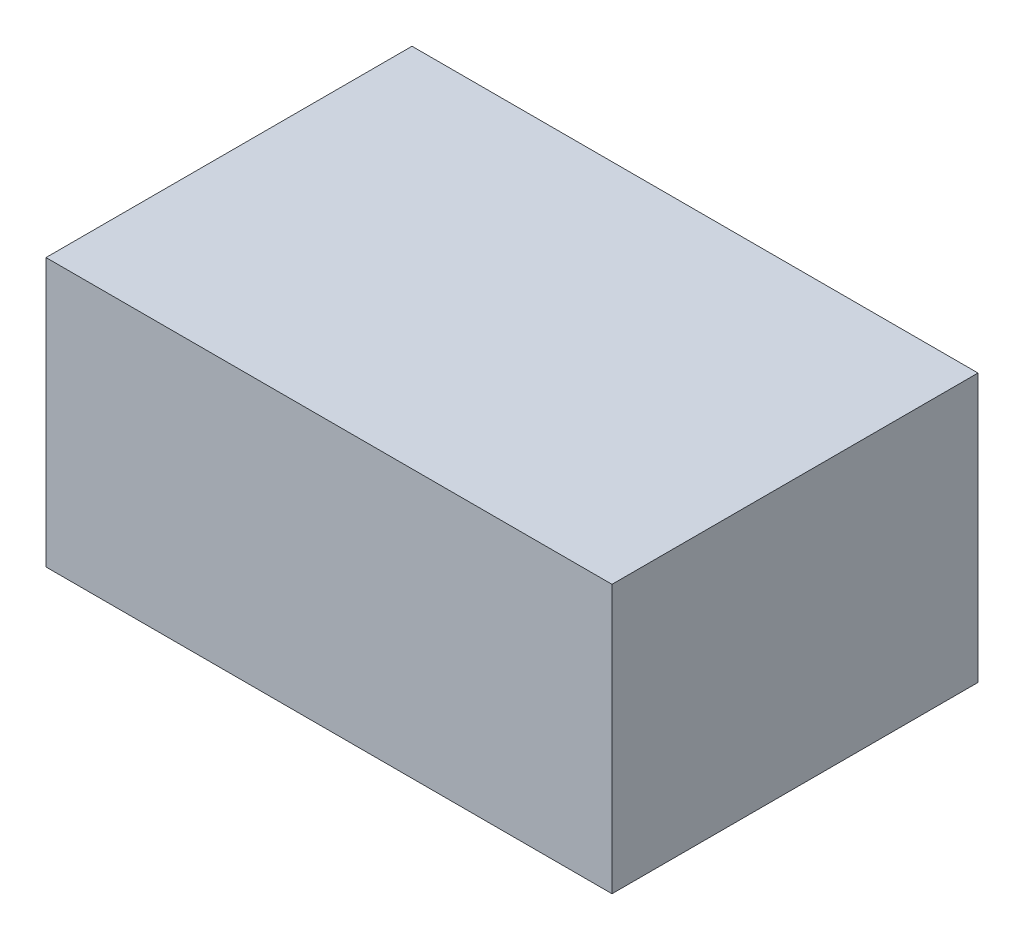
SolidWorks part; units mm, degrees
material "1060 Alloy"
ref_plane "Front Plane" through (0, 0, 0) normal (0, 0, 1) x (1, 0, 0)
ref_plane "Top Plane" through (0, 0, 0) normal (0, 1, 0) x (1, 0, 0)
ref_plane "Right Plane" through (0, 0, 0) normal (1, 0, 0) x (0, 0, -1)
sketch "Sketch1" plane through (0, 0, 0) normal (0, 0, 1) x (1, 0, 0)
  line L1 (0, 0) -> (71.882, 0)
  line L2 (0, 0) -> (0, 34.036)
  line L3 (0, 34.036) -> (71.882, 34.036)
  line L4 (71.882, 0) -> (71.882, 34.036)
  dimension "D1" = 71.882
  dimension "D2" = 34.036
extrude "Boss-Extrude1" add sketch "Sketch1" along normal blind 46.482
